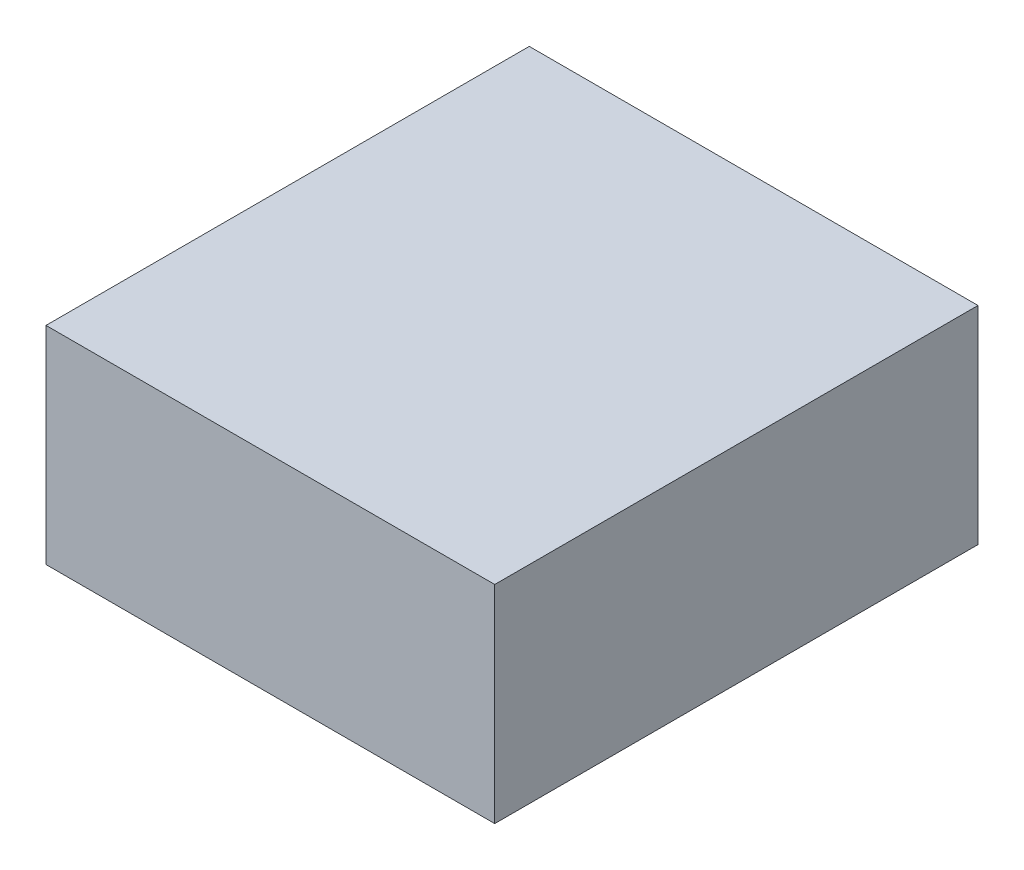
SolidWorks part; units mm, degrees
ref_plane "Front Plane" through (0, 0, 0) normal (0, 0, 1) x (1, 0, 0)
ref_plane "Top Plane" through (0, 0, 0) normal (0, 1, 0) x (1, 0, 0)
ref_plane "Right Plane" through (0, 0, 0) normal (1, 0, 0) x (0, 0, -1)
sketch "Sketch1" plane through (0, 0, 0) normal (0, 1, 0) x (1, 0, 0)
  line L1 (0, 0) -> (82.55, 0)
  line L2 (0, 0) -> (0, 88.9)
  line L3 (0, 88.9) -> (82.55, 88.9)
  line L4 (82.55, 0) -> (82.55, 88.9)
  dimension "D1" = 88.9
  dimension "D2" = 82.55
extrude "Boss-Extrude1" add sketch "Sketch1" along normal blind 38.1
